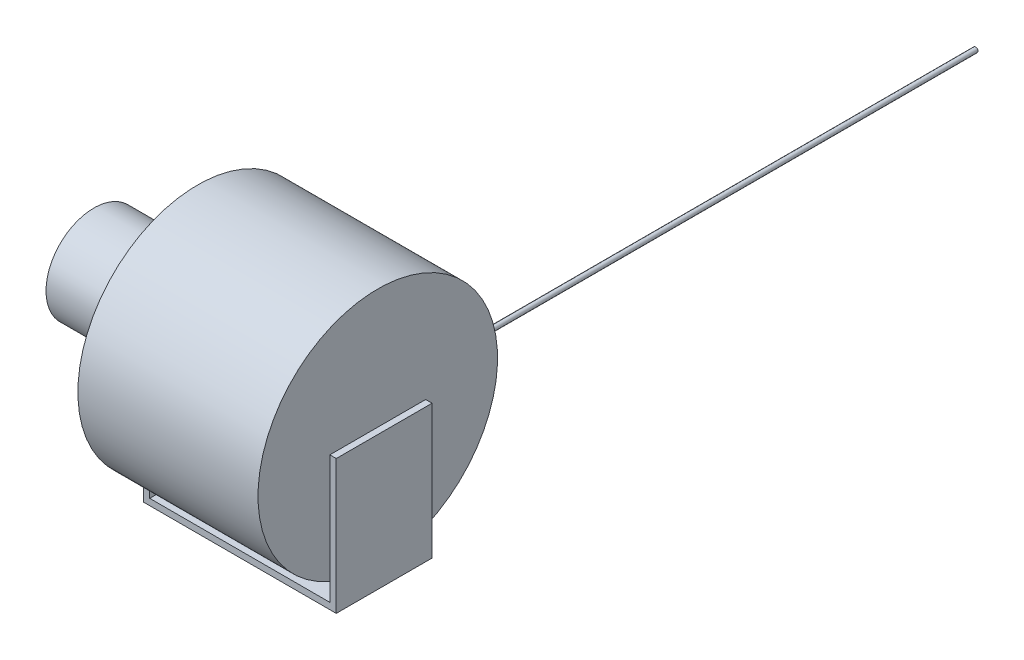
SolidWorks part; units mm, degrees
ref_plane "Front Plane" through (0, 0, 0) normal (0, 0, 1) x (1, 0, 0)
ref_plane "Top Plane" through (0, 0, 0) normal (0, 1, 0) x (1, 0, 0)
ref_plane "Right Plane" through (0, 0, 0) normal (1, 0, 0) x (0, 0, -1)
sketch "Sketch1" plane through (0, 0, 0) normal (1, 0, 0) x (0, 0, -1)
  circle A0 centre (0, 0) radius 187.5
  dimension "D1" = 375
extrude "Boss-Extrude1" add sketch "Sketch1" along normal blind 282
sketch "Sketch2" plane through (0, 0, 0) normal (-1, 0, 0) x (0, 0, 1)
  line L0 (-75, 0) -> (75, 0)
  line L1 (-75, 0) -> (-75, -210)
  line L2 (75, 0) -> (75, -210)
  line L3 (-75, -210) -> (75, -210)
  dimension "D1" = 150
  dimension "D2" = 75
  dimension "D3" = 210
extrude "Boss-Extrude2" add sketch "Sketch2" along normal blind 10
sketch "Sketch3" plane through (282, 0, 0) normal (1, 0, 0) x (0, 0, -1)
  line L0 (-75, 0) -> (75, 0)
  line L1 (-75, 0) -> (-75, -210)
  line L2 (75, 0) -> (75, -210)
  line L3 (-75, -210) -> (75, -210)
  dimension "D1" = 75
  dimension "D2" = 150
  dimension "D3" = 210
extrude "Boss-Extrude3" add sketch "Sketch3" along normal blind 10
sketch "Sketch4" plane through (0, 0, 0) normal (1, 0, 0) x (0, 0, -1)
  line L0 (75, -210) -> (-75, -210)
  line L1 (75, -210) -> (75, -200)
  line L2 (-75, -210) -> (-75, -200)
  line L3 (75, -200) -> (-75, -200)
  dimension "D1" = 10
extrude "Boss-Extrude4" add sketch "Sketch4" along normal up to next
sketch "Sketch5" plane through (-10, 0, 0) normal (-1, 0, 0) x (0, 0, 1)
  circle A0 centre (0, 0) radius 75
  dimension "D1" = 150
extrude "Boss-Extrude5" add sketch "Sketch5" along normal blind 152.4
ref_plane "Plane1" through (50.7, 0, 0) normal (1, 0, 0) x (0, 0, -1)
sketch "Sketch6" plane through (50.7, 0, 0) normal (1, 0, 0) x (0, 0, -1)
  line L0 (0, 0) -> (0, -187.5) construction
  line L1 (0, -187.5) -> (200, -187.5)
  dimension "D1" = 187.5
  dimension "D2" = 200
ref_plane "Plane2" through (0, 0, -200) normal (0, 0, -1) x (-1, 0, 0)
sketch "Sketch7" plane through (0, 0, -200) normal (0, 0, -1) x (-1, 0, 0)
  circle A0 centre (-50.7, -187.5) radius 3.8
  dimension "D1" = 7.6
sweep "Sweep1" add profiles "Sketch7" path "Sketch6"
sketch "Sketch8" plane through (0, 0, -200) normal (0, 0, -1) x (-1, 0, 0)
  circle A0 centre (-50.7, -187.5) radius 3.8
extrude "Boss-Extrude6" add sketch "Sketch8" along normal blind 967.2
